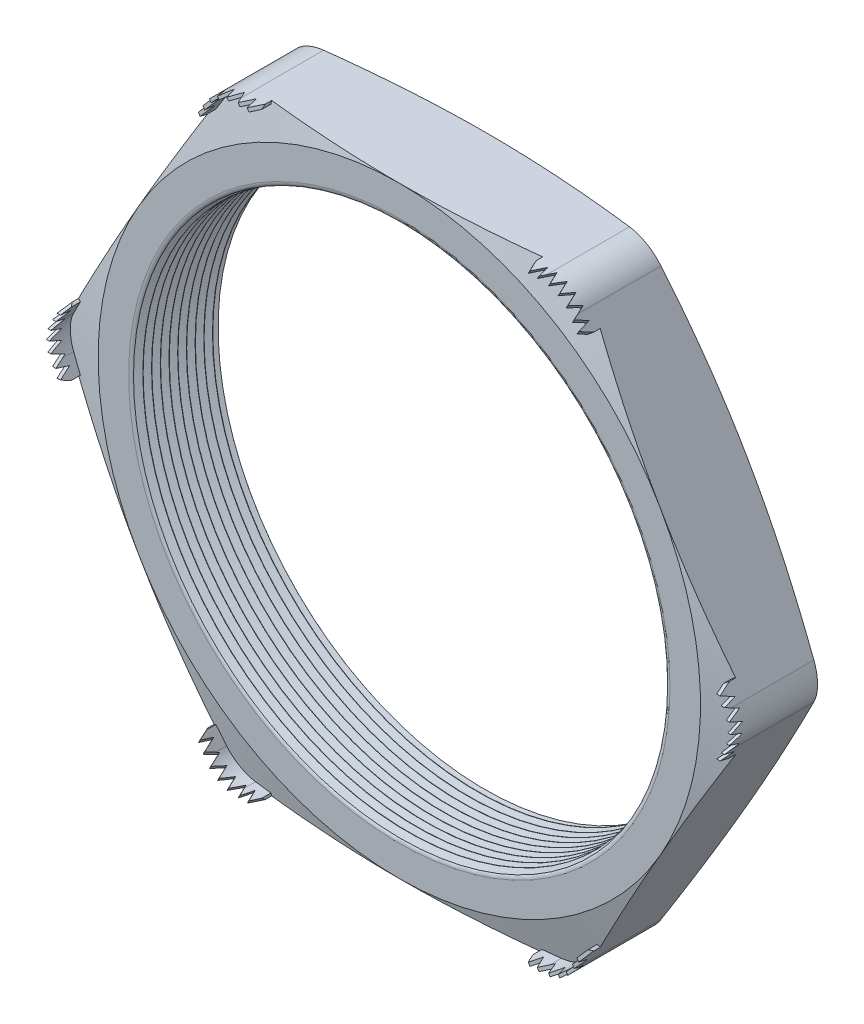
SolidWorks part; units mm, degrees
ref_plane "Front Plane" through (0, 0, 0) normal (0, 0, 1) x (1, 0, 0)
ref_plane "Top Plane" through (0, 0, 0) normal (0, 1, 0) x (1, 0, 0)
ref_plane "Right Plane" through (0, 0, 0) normal (1, 0, 0) x (0, 0, -1)
sketch "Sketch1" plane through (0, 0, 0) normal (0, 0, 1) x (1, 0, 0)
  line L1 (-12.1717, 0) -> (-6.0858, -10.541)
  line L2 (-6.0858, -10.541) -> (6.0858, -10.541)
  line L3 (6.0858, -10.541) -> (12.1717, 0)
  line L4 (12.1717, 0) -> (6.0858, 10.541)
  line L5 (6.0858, 10.541) -> (-6.0858, 10.541)
  line L6 (-6.0858, 10.541) -> (-12.1717, 0)
  circle A0 centre (0, 0) radius 10.541 construction
  circle A1 centre (0, 0) radius 9.271
  dimension "TS" = 18.542
  dimension "H" = 21.082
extrude "Extrude1" add sketch "Sketch1" along normal blind 3.048
fillet "Fillet1" radius 1.27 6 edges at (-6.0858, 10.541, 1.524) (-12.1717, 0, 1.524) (-6.0858, -10.541, 1.524) (6.0858, -10.541, 1.524) (12.1717, 0, 1.524) (6.0858, 10.541, 1.524)
sketch "Sketch2" plane through (0, 0, 3.048) normal (0, 0, 1) x (1, 0, 0)
  line L0 (-5.3526, 10.541) -> (-4.743, 10.541)
  line L1 (5.3526, 10.541) -> (-5.3526, 10.541) construction
  line L2 (-6.4525, 9.906) -> (-6.7573, 9.3781)
  line L3 (-6.4525, 9.906) -> (-11.8051, 0.635) construction
  line L4 (-5.3526, 10.4394) -> (-4.743, 10.4394)
  line L5 (-6.3645, 9.8552) -> (-6.6693, 9.3273)
  line L6 (-6.7573, 9.3781) -> (-6.6693, 9.3273)
  line L7 (-4.743, 10.541) -> (-4.743, 10.4394)
  arc A0 (-5.3526, 10.4394) -> (-6.3645, 9.8552) centre (-5.3526, 9.271) ccw
  arc A1 (-5.3526, 10.541) -> (-6.4525, 9.906) centre (-5.3526, 9.271) ccw construction
  arc A4 (-5.3526, 10.541) -> (-6.4525, 9.906) centre (-5.3526, 9.271) ccw
  dimension "D1" = 0.6096
  dimension "D2" = 0.6096
  dimension "OFFSET" = 0.1016
fillet "Fillet3" radius 0.2032 2 edges at (9.271, 0, 0) (9.271, 0, 3.048)
sketch "Sketch3" plane through (0, 0, 0) normal (0, 1, 0) x (1, 0, 0)
  line L0 (-9.271, -3.048) -> (-9.271, -2.7547)
  line L2 (-9.271, -2.7547) -> (-9.525, -2.9014)
  line L3 (-9.525, -2.9014) -> (-9.271, -3.048)
  line L4 (-9.271, -0.2032) -> (-9.271, -2.8448) construction
  line L5 (-6.4525, -3.048) -> (-11.8051, -3.048) construction
  dimension "D1" = 60
  dimension "D2" = 60
  dimension "D3" = 0.254
revolve "Cut-Revolve1" cut sketch "Sketch3" angle 360 about axis through (0, 0, 3.048) along (0, 0, -1)
pattern_linear "LPattern1" count 10 spacing 0.3048 along (0, 0, -1) of "Cut-Revolve1"
sketch "Sketch4" plane through (0, 0, 0) normal (0, 0, -1) x (-1, 0, 0)
  line L0 (-11.8051, 0.635) -> (-6.4525, 9.906) construction
  circle A0 centre (0, 0) radius 10.541
extrude "Cut-Extrude1" cut sketch "Sketch4" against normal through all draft 75 flip side to cut
sketch "Sketch5" plane through (0, 0, 3.048) normal (0, 0, 1) x (1, 0, 0)
  line L0 (5.3526, 10.541) -> (-5.3526, 10.541) construction
  circle A0 centre (0, 0) radius 10.541
extrude "Cut-Extrude2" cut sketch "Sketch5" against normal through all draft 75 flip side to cut
extrude "Extrude2" add sketch "Sketch2" along normal blind 1.016 and the other way up to next
ref_plane "Plane1" through (-5.7061, 9.8833, 0) normal (0.5, -0.866, 0) x (0.866, 0.5, 0)
sketch "Sketch7" plane through (-5.7061, 9.8833, 0) normal (0.5, -0.866, 0) x (0.866, 0.5, 0)
  line L0 (-1.1629, 2.9972) -> (-0.9851, 3.4239)
  line L1 (-1.1629, 2.7752) -> (-1.1629, 4.064) construction
  line L2 (0, 1.3136) -> (0, 4.0135) construction
  line L4 (-0.9851, 3.4239) -> (-0.8073, 2.9972)
  line L5 (-0.3556, 3.4239) -> (-0.1778, 2.9972)
  line L6 (-0.7112, 3.4239) -> (-0.5334, 2.9972)
  line L7 (-0.1778, 2.9972) -> (0, 3.4239)
  line L8 (0, 3.4239) -> (0.1778, 2.9972)
  line L10 (0.3556, 3.4239) -> (0.5334, 2.9972)
  line L11 (0.7112, 3.4239) -> (0.889, 2.9972)
  line L12 (-0.8073, 2.9972) -> (-0.7112, 3.4239)
  line L13 (-0.5334, 2.9972) -> (-0.3556, 3.4239)
  line L14 (0.1778, 2.9972) -> (0.3556, 3.4239)
  line L15 (0.9851, 3.4239) -> (1.1629, 2.9972)
  line L16 (1.1629, 2.7752) -> (1.1629, 4.064) construction
  line L17 (-1.1629, 2.9972) -> (-1.1629, 4.064)
  line L19 (-1.1629, 4.064) -> (1.1629, 4.064)
  line L20 (1.1629, 4.064) -> (1.1629, 2.9972)
  line L23 (0.5334, 2.9972) -> (0.7112, 3.4239)
  line L25 (0.889, 2.9972) -> (0.9851, 3.4239)
  dimension "D1" = 1.0668
  dimension "D2" = 0.6401
  dimension "D3" = 0.1778
extrude "Cut-Extrude4" cut sketch "Sketch7" against normal through all
pattern_circular "CirPattern1" count 6 over 360 about axis through (0, 0, 0) along (0, 0, 1) of "Extrude2"
pattern_circular "CirPattern2" count 6 over 360 about axis through (0, 0, 0) along (0, 0, 1) of "Cut-Extrude4"
